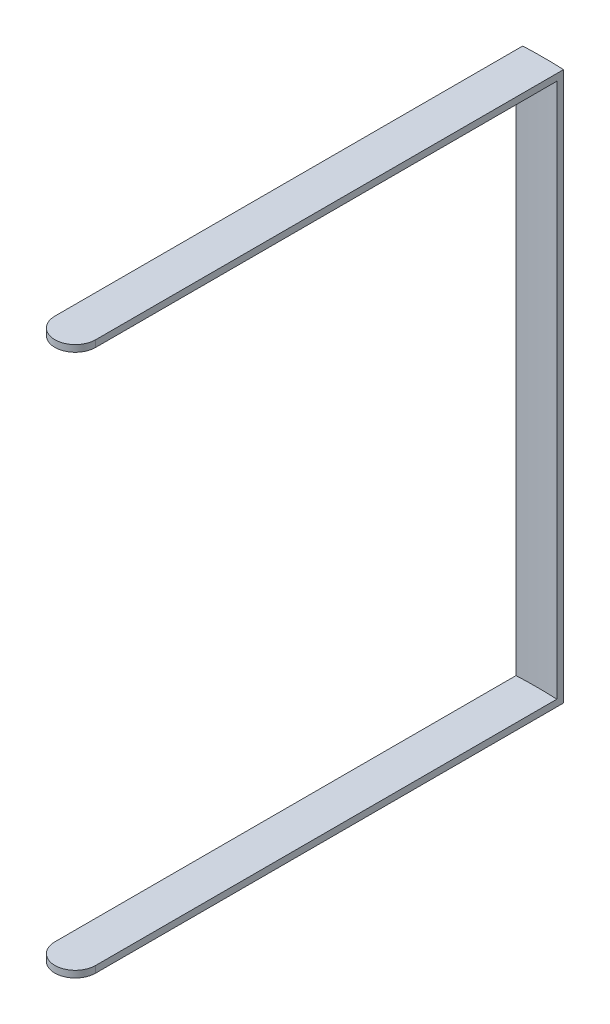
SolidWorks part; units mm, degrees
ref_plane "Front Plane" through (0, 0, 0) normal (0, 0, 1) x (1, 0, 0)
ref_plane "Top Plane" through (0, 0, 0) normal (0, 1, 0) x (1, 0, 0)
ref_plane "Right Plane" through (0, 0, 0) normal (1, 0, 0) x (0, 0, -1)
sketch "Sketch1" plane through (0, 0, 0) normal (0, 1, 0) x (1, 0, 0)
  line L0 (-7.7555, 0) -> (-7.7555, 177.6308)
  line L1 (7.7555, 0) -> (7.7555, 177.6308)
  line L2 (-7.7555, 177.6308) -> (0, 0) construction
  line L3 (0, 0) -> (7.7555, 177.6308) construction
  arc A0 (7.7555, 0) -> (-7.7555, 0) centre (0, 0) cw
  arc A1 (-7.7555, 177.6308) -> (7.7555, 177.6308) centre (0, 0) cw
  dimension "D2" = 177.8
  dimension "D1" = 5
extrude "Boss-Extrude1" add sketch "Sketch1" along normal blind 2.54
sketch "Sketch2" plane through (0, 2.54, 0) normal (0, 1, 0) x (1, 0, 0)
  line L0 (-7.7555, 177.6308) -> (-7.7555, 0) construction
  line L1 (7.7555, 0) -> (7.7555, 177.6308) construction
  line L2 (-7.7555, 177.6308) -> (-7.7555, 175.0908)
  line L3 (7.7555, 175.0908) -> (7.7555, 177.6308)
  arc A0 (-7.7555, 177.6308) -> (7.7555, 177.6308) centre (0, 0) cw
  arc A1 (7.7555, 177.6308) -> (-7.7555, 177.6308) centre (0, 0) ccw construction
  arc A2 (-7.7555, 175.0908) -> (7.7555, 175.0908) centre (0, 0) cw
  dimension "D1" = 2.54
extrude "Boss-Extrude2" add sketch "Sketch2" along normal blind 203.2
sketch "Sketch3" plane through (0, 205.74, 0) normal (0, 1, 0) x (1, 0, 0)
  line L0 (-7.7555, 0) -> (-7.7555, 177.6308)
  line L1 (7.7555, 0) -> (7.7555, 177.6308)
  arc A0 (7.7555, 0) -> (-7.7555, 0) centre (0, 0) cw
  arc A1 (-7.7555, 177.6308) -> (7.7555, 177.6308) centre (0, 0) cw
  arc A2 (7.7555, 177.6308) -> (-7.7555, 177.6308) centre (0, 0) ccw construction
  point P8 (-6.702, 177.6736)
extrude "Boss-Extrude3" add sketch "Sketch3" along normal blind 2.54
